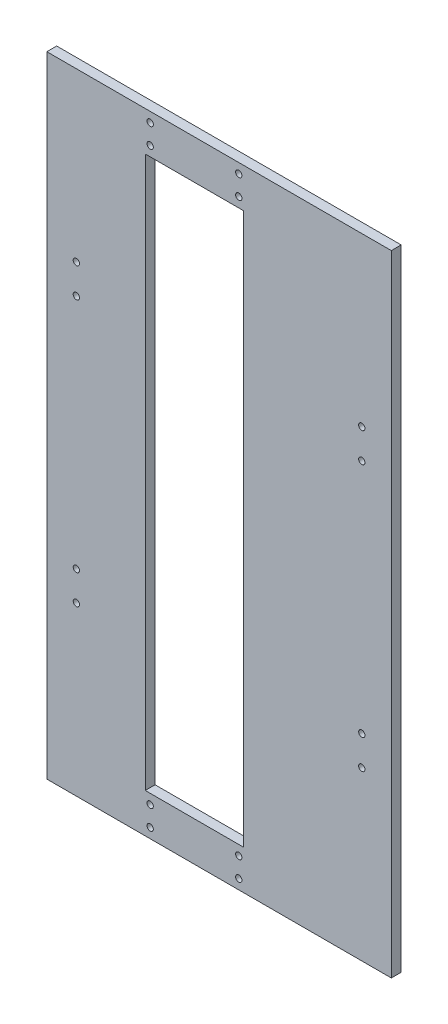
SolidWorks part; units mm, degrees
ref_plane "Front Plane" through (0, 0, 0) normal (0, 0, 1) x (1, 0, 0)
ref_plane "Top Plane" through (0, 0, 0) normal (0, 1, 0) x (1, 0, 0)
ref_plane "Right Plane" through (0, 0, 0) normal (1, 0, 0) x (0, 0, -1)
sketch "Sketch1" plane through (0, 0, 0) normal (0, 0, 1) x (1, 0, 0)
  line L0 (-22.5, 145) -> (-22.5, 155) construction
  line L1 (22.5, -145) -> (-22.5, -145) construction
  line L2 (22.5, -145) -> (22.5, 145) construction
  line L3 (22.5, 145) -> (-22.5, 145) construction
  line L4 (-22.5, -145) -> (-22.5, 145) construction
  line L5 (22.5, -145) -> (-22.5, 145) construction
  line L6 (22.5, 145) -> (-22.5, -145) construction
  line L8 (50, 160) -> (-50, 160)
  line L9 (50, 160) -> (50, -160)
  line L10 (50, -160) -> (-50, -160)
  line L11 (-50, 160) -> (-50, -160)
  line L12 (50, 160) -> (-50, -160) construction
  line L13 (50, -160) -> (-50, 160) construction
  line L14 (25, -140) -> (-25, -140)
  line L15 (25, -140) -> (25, 140)
  line L16 (25, 140) -> (-25, 140)
  line L17 (-25, -140) -> (-25, 140)
  line L18 (25, -140) -> (-25, 140) construction
  line L19 (25, 140) -> (-25, -140) construction
  circle A0 centre (-22.5, 145) radius 1.6
  circle A1 centre (-22.5, 155) radius 1.6
  circle A2 centre (22.5, 145) radius 1.6
  circle A3 centre (22.5, -145) radius 1.6
  circle A4 centre (-22.5, -145) radius 1.6
  circle A8 centre (22.5, 155) radius 1.6
  circle A9 centre (22.5, -155) radius 1.6
  circle A10 centre (-22.5, -155) radius 1.6
  point P0 (0, 0)
  point P9 (0, 0)
  point P26 (0, 0)
  dimension "D4" = 3.2
  dimension "D5" = 3.2
  dimension "D1" = 45
  dimension "D2" = 290
  dimension "D3" = 10
  dimension "D10" = 100
  dimension "D11" = 320
  dimension "D12" = 50
  dimension "D13" = 280
  dimension "D6" = 2
  dimension "D7" = 2
  dimension "D8" = 2
  dimension "D9" = 2
extrude "Boss-Extrude1" add sketch "Sketch1" along normal blind 5
sketch "Sketch2" plane through (0, 0, 0) normal (0, 0, 1) x (1, 0, 0)
  line L1 (50, -160) -> (100, -160)
  line L2 (50, -160) -> (50, 160)
  line L3 (50, 160) -> (100, 160)
  line L4 (100, -160) -> (100, 160)
  dimension "D1" = 50
extrude "Boss-Extrude2" add sketch "Sketch2" along normal blind 5
sketch "Sketch3" plane through (0, 0, 0) normal (0, 0, 1) x (1, 0, 0)
  line L1 (-50, -160) -> (-75, -160)
  line L2 (-50, -160) -> (-50, 160)
  line L3 (-50, 160) -> (-75, 160)
  line L4 (-75, -160) -> (-75, 160)
  dimension "D1" = 25
  dimension "D2" = 320
extrude "Boss-Extrude3" add sketch "Sketch3" along normal blind 5
sketch "Sketch4" plane through (0, 0, 5) normal (0, 0, 1) x (1, 0, 0)
  line L0 (-75, 0) -> (-60, 0) construction
  line L1 (-75, 160) -> (-75, -160) construction
  line L2 (-60, 0) -> (-60, 60) construction
  line L3 (-60, 60) -> (-60, 75) construction
  line L4 (12.5, 160) -> (12.5, 104.0828) construction
  line L5 (100, 160) -> (-75, 160) construction
  circle A0 centre (-60, 75) radius 1.6
  circle A1 centre (-60, 60) radius 1.6
  circle A2 centre (-60, -60) radius 1.6
  circle A3 centre (-60, -75) radius 1.6
  circle A4 centre (85, -75) radius 1.6
  circle A5 centre (85, -60) radius 1.6
  circle A6 centre (85, 60) radius 1.6
  circle A7 centre (85, 75) radius 1.6
  dimension "D4" = 3.2
  dimension "D5" = 3.2
  dimension "D1" = 15
  dimension "D2" = 15
  dimension "D3" = 60
extrude "Cut-Extrude1" cut sketch "Sketch4" against normal up to next
